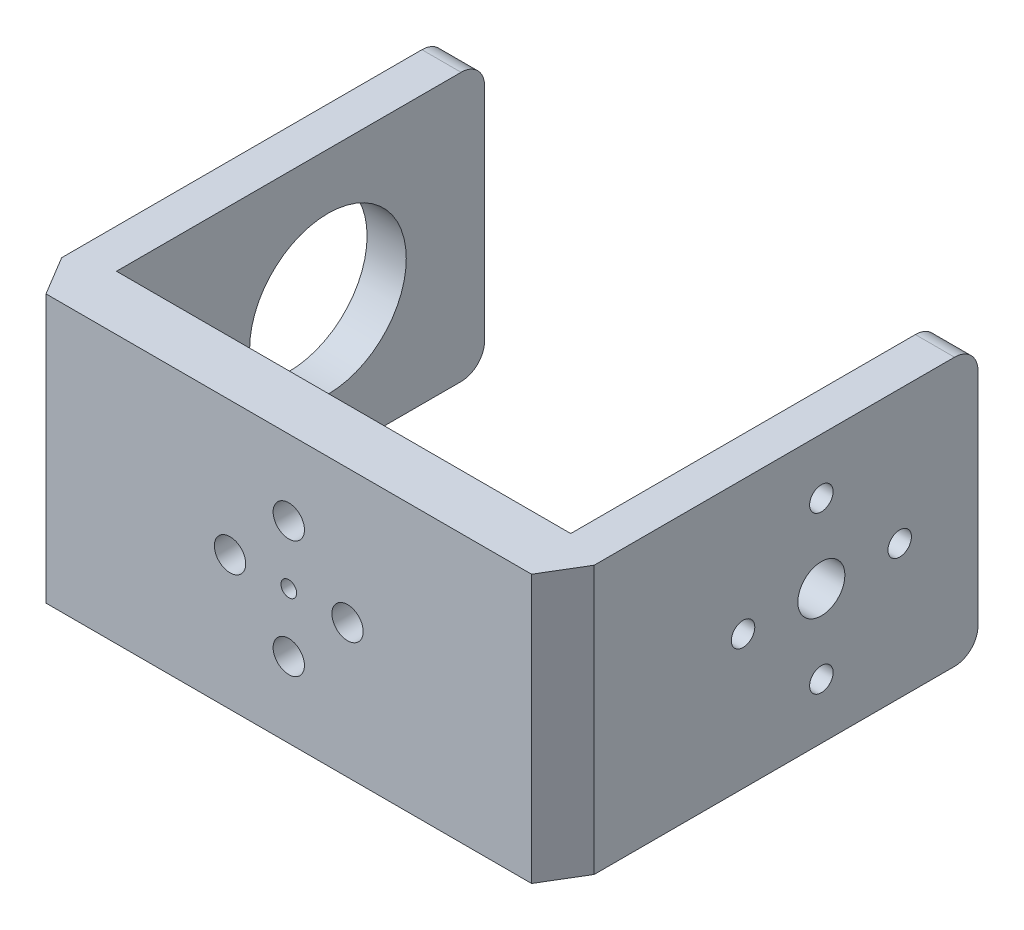
SolidWorks part; units mm, degrees
ref_plane "Front Plane" through (0, 0, 0) normal (0, 0, 1) x (1, 0, 0)
ref_plane "Top Plane" through (0, 0, 0) normal (0, 1, 0) x (1, 0, 0)
ref_plane "Right Plane" through (0, 0, 0) normal (1, 0, 0) x (0, 0, -1)
sketch "Sketch1" plane through (0, 0, 0) normal (0, 1, 0) x (1, 0, 0)
  line L0 (0, 0) -> (58, 0)
  line L1 (58, 0) -> (58, 47)
  line L2 (0, 0) -> (0, 47)
  line L3 (0, -7) -> (58, -7)
  line L4 (0, 47) -> (-5, 47)
  line L9 (58, 47) -> (63, 47)
  line L12 (58, -7) -> (60, -7)
  line L14 (0, -7) -> (-2, -7)
  line L16 (-5, 47) -> (-5, -2)
  line L17 (-5, -2) -> (-2, -7)
  line L18 (63, 47) -> (63, -2)
  line L19 (63, -2) -> (60, -7)
  dimension "D1" = 58
  dimension "D2" = 47
  dimension "D3" = 47
  dimension "D4" = 58
  dimension "D5" = 7
  dimension "D6" = 5
  dimension "D7" = 49
  dimension "D8" = 49
  dimension "D9" = 2
  dimension "D10" = 5
  dimension "D13" = 2
extrude "Boss-Extrude1" add sketch "Sketch1" along normal blind 34.2
sketch "Sketch4" plane through (0, 0, 0) normal (0, 0, -1) x (-1, 0, 0)
  line L0 (-29, 34.2) -> (-29, 0)
  line L1 (-58, 34.2) -> (0, 34.2) construction
  line L2 (-58, 0) -> (0, 0) construction
  circle A0 centre (-29, 17.1) radius 7.5
  circle A1 centre (-29, 24.6) radius 2
  circle A2 centre (-36.5, 17.1) radius 2
  circle A3 centre (-21.5, 17.1) radius 2
  circle A4 centre (-29, 9.6) radius 2
  circle A5 centre (-29, 17.1) radius 1
  dimension "D1" = 15
  dimension "D2" = 4
  dimension "D3" = 4
  dimension "D4" = 4
  dimension "D5" = 4
  dimension "D6" = 2
extrude "Cut-Extrude3" cut sketch "Sketch4" against normal up to surface (7 mm away) contours A3 | A4 | A2 | A1 | A5 up to face at (29, 17.1, 7)
fillet "Fillet1" radius 3 4 edges at (-2.5, 0, -47) (-2.5, 34.2, -47) (60.5, 0, -47) (60.5, 34.2, -47)
sketch "Sketch5" plane through (-5, 0, 0) normal (-1, 0, 0) x (0, 0, 1)
  line L0 (-27, 34.2) -> (-27, 0)
  line L1 (-44, 34.2) -> (2, 34.2) construction
  line L2 (-44, 0) -> (2, 0) construction
  line L3 (2, 34.2) -> (2, 0) construction
  circle A0 centre (-27, 17.1) radius 10
  dimension "D2" = 20
  dimension "D1" = 29
extrude "Cut-Extrude4" cut sketch "Sketch5" against normal up to surface (5 mm away) contours A0 up to face at (0, 17.1, -30.5404)
sketch "Sketch6" plane through (63, 0, 0) normal (1, 0, 0) x (0, 0, -1)
  line L0 (27, 34.2) -> (27, 0)
  line L1 (-2, 34.2) -> (44, 34.2) construction
  line L2 (-2, 0) -> (44, 0) construction
  line L3 (-2, 34.2) -> (-2, 0) construction
  circle A0 centre (27, 17.1) radius 3
  circle A1 centre (27, 17.1) radius 10
  circle A2 centre (27, 27.1) radius 1.5
  circle A3 centre (37, 17.1) radius 1.5
  circle A4 centre (27, 7.1) radius 1.5
  circle A5 centre (17, 17.1) radius 1.5
  dimension "D2" = 6
  dimension "D3" = 20
  dimension "D4" = 3
  dimension "D5" = 3
  dimension "D6" = 3
  dimension "D7" = 3
  dimension "D1" = 29
extrude "Cut-Extrude5" cut sketch "Sketch6" against normal up to surface (5 mm away) contours A2 | A3 | A0 | A4 | A5 up to face at (58, 17.1, -30.5404)
